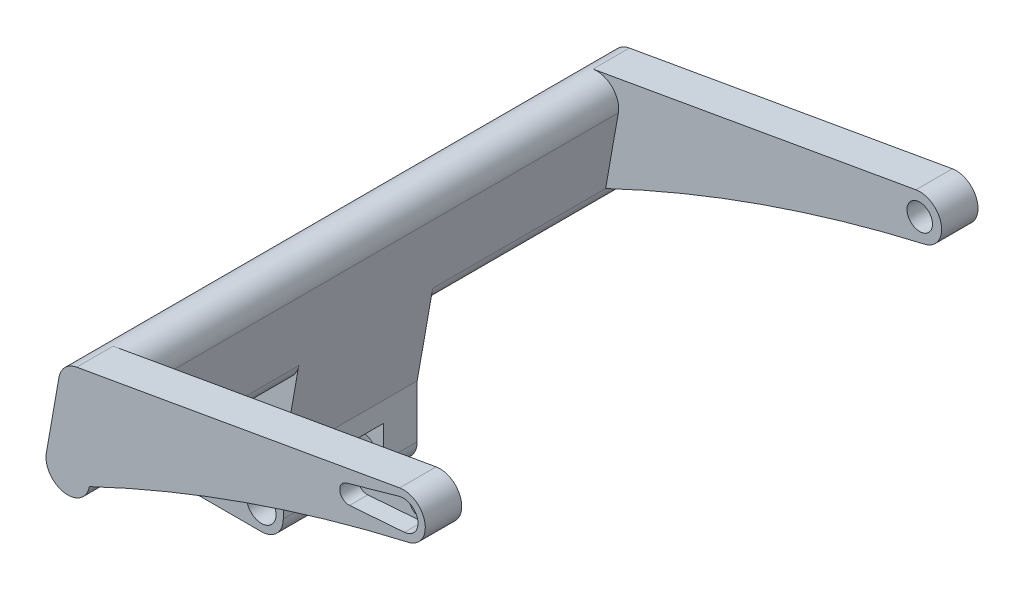
SolidWorks part; units mm, degrees
ref_plane "Front Plane" through (0, 0, 0) normal (0, 0, 1) x (1, 0, 0)
ref_plane "Top Plane" through (0, 0, 0) normal (0, 1, 0) x (1, 0, 0)
ref_plane "Right Plane" through (0, 0, 0) normal (1, 0, 0) x (0, 0, -1)
sketch "Sketch1" plane through (0, 0, 0) normal (0, 0, 1) x (1, 0, 0)
  line L0 (0, 0) -> (45.64, 0) construction
  line L1 (22.82, 0) -> (22.82, 11) construction
  line L2 (0, -6) -> (45.64, -6)
  line L3 (45.64, 15) -> (53.4542, 59.3163) construction
  line L4 (39.7312, 16.0419) -> (47.5453, 60.3582)
  line L5 (51.5488, 13.9581) -> (59.363, 58.2745)
  line L6 (51.64, 0) -> (51.64, 15)
  line L15 (37.3623, 73.318) -> (36.5541, 72.5097)
  circle A0 centre (0, 0) radius 4.025
  circle A1 centre (22.82, 11) radius 4.025
  circle A2 centre (0, 0) radius 6
  circle A3 centre (22.82, 11) radius 7.308
  arc A4 (0, 6) -> (16.7133, 15.0143) centre (0, 26.001) ccw
  arc A5 (22.82, 18.308) -> (43.1367, 35.3557) centre (22.82, 38.9381) ccw
  circle A6 centre (45.64, 0) radius 6
  circle A7 centre (45.64, 0) radius 4.025
  arc A8 (39.7312, 16.0419) -> (51.5488, 13.9581) centre (45.64, 15) ccw
  arc A9 (59.363, 58.2745) -> (47.5453, 60.3582) centre (53.4542, 59.3163) ccw
  point P21 (49.5471, 37.1582)
  point P28 (0, 0)
  point P29 (51.2782, 17.0521)
  point P30 (0, 0)
  point P31 (0, 0)
  point P32 (51.6191, 14.5)
  dimension "D1" = 8.05
  dimension "D4" = 12
  dimension "D8" = 14.616
  dimension "D2" = 45.64
  dimension "D3" = 11
  dimension "D5" = 80
  dimension "D6" = 45
  dimension "D7" = 15
extrude "Boss-Extrude2" add sketch "Sketch1" along normal blind 36.76
ref_plane "Plane4" through (0, 0, 9.19) normal (0, 0, -1) x (-1, 0, 0)
sketch "Sketch4" plane through (0, 0, 9.19) normal (0, 0, -1) x (-1, 0, 0)
  line L0 (0, -6) -> (-45.64, -6) construction
  line L1 (0, -6) -> (-45.64, -6)
  line L2 (-45.64, 0) -> (0, 0) construction
  line L3 (-45.64, 6) -> (0, 6)
  line L4 (-45.64, -6) -> (0, -6)
  circle A0 centre (-22.82, 11) radius 4.025 construction
  circle A1 centre (0, 0) radius 4.025 construction
  circle A2 centre (-45.64, 0) radius 4.025 construction
  circle A3 centre (-22.82, 11) radius 4.025
  circle A4 centre (0, 0) radius 4.025
  circle A5 centre (-45.64, 0) radius 4.025
  arc A6 (0, -6) -> (0, 6) centre (0, 0) ccw construction
  arc A7 (-16.7133, 15.0143) -> (0, 6) centre (0, 26.001) ccw construction
  arc A8 (0, -6) -> (0, 6) centre (0, 0) ccw
  arc A9 (-16.7133, 15.0143) -> (0, 6) centre (0, 26.001) ccw
  arc A10 (-45.64, 6) -> (-45.64, -6) centre (-45.64, 0) ccw
  arc A11 (0, -6) -> (0, 6) centre (0, 0) ccw
  circle A12 centre (-22.82, 11) radius 7.308
  arc A13 (-45.64, 6) -> (-28.9267, 15.0143) centre (-45.64, 26.001) ccw
  point P12 (-22.82, 0)
sketch "Sketch5" plane through (0, 0, 36.76) normal (0, 0, 1) x (1, 0, 0)
  line L0 (53.4542, 59.3163) -> (49.9812, 39.6202) construction
  line L1 (59.363, 58.2745) -> (55.8901, 38.5783)
  line L2 (47.5453, 60.3582) -> (44.0724, 40.6621)
  line L3 (51.64, 14.4751) -> (59.363, 58.2745) construction
  line L4 (51.64, 14.4751) -> (59.363, 58.2745)
  line L5 (43.1367, 35.3557) -> (47.5453, 60.3582) construction
  line L6 (43.1367, 35.3557) -> (47.5453, 60.3582)
  arc A0 (59.363, 58.2745) -> (47.5453, 60.3582) centre (53.4542, 59.3163) ccw
  arc A1 (44.0724, 40.6621) -> (55.8901, 38.5783) centre (49.9812, 39.6202) ccw
  arc A2 (59.363, 58.2745) -> (47.5453, 60.3582) centre (53.4542, 59.3163) ccw construction
  arc A3 (59.363, 58.2745) -> (47.5453, 60.3582) centre (53.4542, 59.3163) ccw
  point P3 (51.7177, 49.4683)
  dimension "D1" = 20
extrude "Ride-Side-Extrude" add sketch "Sketch5" along normal blind 57.47
sketch "Sketch7" plane through (0, 0, 0) normal (0, 0, -1) x (-1, 0, 0)
  line L0 (-53.4542, 59.3163) -> (-49.9812, 39.6202) construction
  line L1 (-47.5453, 60.3582) -> (-44.0724, 40.6621)
  line L2 (-59.363, 58.2745) -> (-55.8901, 38.5783)
  line L3 (-43.1367, 35.3557) -> (-47.5453, 60.3582) construction
  line L4 (-43.1367, 35.3557) -> (-47.5453, 60.3582)
  line L5 (-51.64, 14.4751) -> (-59.363, 58.2745) construction
  line L6 (-51.64, 14.4751) -> (-59.363, 58.2745)
  arc A0 (-47.5453, 60.3582) -> (-59.363, 58.2745) centre (-53.4542, 59.3163) ccw
  arc A1 (-55.8901, 38.5783) -> (-44.0724, 40.6621) centre (-49.9812, 39.6202) ccw
  arc A2 (-47.5453, 60.3582) -> (-59.363, 58.2745) centre (-53.4542, 59.3163) ccw construction
  arc A3 (-47.5453, 60.3582) -> (-59.363, 58.2745) centre (-53.4542, 59.3163) ccw
  point P3 (-51.7177, 49.4683)
  dimension "D1" = 20
extrude "Left-Side-Extrude" add sketch "Sketch7" along normal blind 57.47
sketch "Sketch16" plane through (0, 0, 94.23) normal (0, 0, 1) x (1, 0, 0)
  line L0 (52.4123, 65.2252) -> (141.045, 80.8535)
  line L1 (47.5453, 60.3582) -> (44.0724, 40.6621) construction
  line L2 (55.8901, 38.5783) -> (59.363, 58.2745) construction
  line L3 (47.5453, 60.3582) -> (44.0724, 40.6621)
  line L4 (55.8901, 38.5783) -> (59.363, 58.2745)
  line L5 (58.6335, 54.137) -> (143.1288, 69.0358)
  arc A0 (59.363, 58.2745) -> (47.5453, 60.3582) centre (53.4542, 59.3163) ccw construction
  arc A1 (59.363, 58.2745) -> (47.5453, 60.3582) centre (53.4542, 59.3163) ccw
  arc A2 (44.0724, 40.6621) -> (55.8901, 38.5783) centre (49.9812, 39.6202) ccw construction
  arc A3 (44.0724, 40.6621) -> (55.8901, 38.5783) centre (49.9812, 39.6202) ccw
  arc A4 (141.045, 80.8535) -> (143.1288, 69.0358) centre (142.0869, 74.9447) cw
  arc A5 (55.8901, 38.5783) -> (143.1288, 69.0358) centre (238.7666, -345.0637) cw
  line M9 (55.8901, 38.5783) -> (59.363, 58.2745)
  arc M10 (59.363, 58.2745) -> (47.5453, 60.3582) centre (53.4542, 59.3163) ccw
  dimension "D4" = 425
  dimension "D1" = 110
  dimension "D2" = 90
  dimension "D3" = 12
extrude "Right-Arm-Extrude" add sketch "Sketch16" against normal blind 10 contours A4 L0 L4 L5 M10 | A5 L5 M9
sketch "Sketch17" plane through (0, 0, 94.23) normal (0, 0, 1) x (1, 0, 0)
  line L0 (52.4123, 65.2252) -> (141.045, 80.8535) construction
  line L1 (52.4123, 65.2252) -> (141.045, 80.8535)
  line L2 (142.0869, 74.9447) -> (127.1178, 72.3052)
  line L3 (126.4428, 74.7124) -> (141.0069, 78.7961)
  line L4 (127.3068, 69.8124) -> (142.3893, 70.9561)
  arc A0 (143.1288, 69.0358) -> (141.045, 80.8535) centre (142.0869, 74.9447) ccw construction
  arc A1 (143.1288, 69.0358) -> (141.045, 80.8535) centre (142.0869, 74.9447) ccw
  circle A2 centre (142.0869, 74.9447) radius 4
  circle A3 centre (127.1178, 72.3052) radius 2.5
  dimension "D1" = 8
  dimension "D2" = 5
  dimension "D3" = 15.2
extrude "Servo-Arm-Cut" cut sketch "Sketch17" against normal blind 5
sketch "Sketch18" plane through (0, 0, 94.23) normal (0, 0, 1) x (1, 0, 0)
  arc A0 (142.3893, 70.9561) -> (141.0069, 78.7961) centre (142.0869, 74.9447) ccw construction
  arc A1 (142.3893, 70.9561) -> (141.0069, 78.7961) centre (142.0869, 74.9447) ccw
  circle A2 centre (142.0869, 74.9447) radius 3.5
  dimension "D1" = 7
extrude "Servo-hole" cut sketch "Sketch18" against normal through all contours A2
extrude "Cut-Extrude2" cut sketch "Sketch4" against normal blind 18.38
sketch "Sketch19" plane through (51.64, 0, 0) normal (1, 0, 0) x (0, 0, -1)
  line L1 (-27.57, 0) -> (-9.19, 0)
  line L2 (-27.57, 0) -> (-27.57, 9)
  line L3 (-27.57, 9) -> (-9.19, 9)
  line L4 (-9.19, 0) -> (-9.19, 9)
  line L5 (-9.19, 0) -> (-9.19, -6) construction
  dimension "D1" = 9
extrude "Cut-Extrude3" cut sketch "Sketch19" against normal through all
ref_plane "Mid-Plane" through (0, 0, 18.38) normal (0, 0, -1) x (-1, 0, 0)
mirror "Left-Arm Extrude" about plane through (0, 0, 18.38) normal (0, 0, -1) of "Servo-hole", "Servo-Arm-Cut", "Right-Arm-Extrude"
